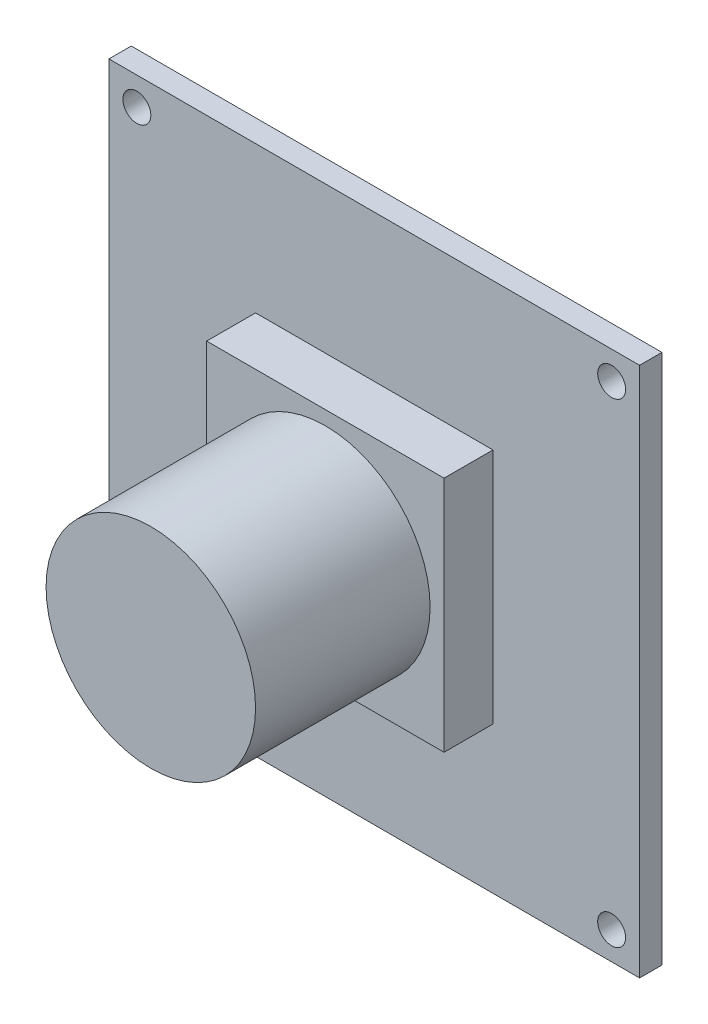
SolidWorks part; units mm, degrees
ref_plane "Front Plane" through (0, 0, 0) normal (0, 0, 1) x (1, 0, 0)
ref_plane "Top Plane" through (0, 0, 0) normal (0, 1, 0) x (1, 0, 0)
ref_plane "Right Plane" through (0, 0, 0) normal (1, 0, 0) x (0, 0, -1)
sketch "Sketch1" plane through (0, 0, 0) normal (0, 0, 1) x (1, 0, 0)
  line L1 (-19, -19) -> (19, -19)
  line L2 (-19, -19) -> (-19, 19)
  line L3 (-19, 19) -> (19, 19)
  line L4 (19, -19) -> (19, 19)
  line L5 (-19, -19) -> (19, 19) construction
  line L6 (-19, 19) -> (19, -19) construction
  point P0 (0, 0)
  dimension "D1" = 38
  dimension "D2" = 38
extrude "Boss-Extrude1" add sketch "Sketch1" against normal blind 1.6
sketch "Sketch2" plane through (0, 0, 0) normal (0, 0, 1) x (1, 0, 0)
  line L1 (-8.5, -8.5) -> (8.5, -8.5)
  line L2 (-8.5, -8.5) -> (-8.5, 8.5)
  line L3 (-8.5, 8.5) -> (8.5, 8.5)
  line L4 (8.5, -8.5) -> (8.5, 8.5)
  line L5 (-8.5, -8.5) -> (8.5, 8.5) construction
  line L6 (-8.5, 8.5) -> (8.5, -8.5) construction
  point P0 (0, 0)
  dimension "D1" = 17
  dimension "D2" = 17
extrude "Boss-Extrude2" add sketch "Sketch2" along normal blind 3.5
sketch "Sketch3" plane through (0, 0, 3.5) normal (0, 0, 1) x (1, 0, 0)
  circle A0 centre (0, 0) radius 7.5
  dimension "D1" = 15
extrude "Boss-Extrude3" add sketch "Sketch3" along normal blind 12.5
sketch "Sketch4" plane through (0, 0, 0) normal (0, 0, 1) x (1, 0, 0)
  line L0 (0, 0) -> (0, 19) construction
  line L1 (19, 19) -> (-19, 19) construction
  line L2 (0, 0) -> (19, 0) construction
  line L3 (19, -19) -> (19, 19) construction
  line L4 (-19, 19) -> (-19, -19) construction
  circle A0 centre (-17, 17) radius 1
  circle A1 centre (17, 17) radius 1
  circle A2 centre (-17, -17) radius 1
  circle A3 centre (17, -17) radius 1
  point P10 (0, 0)
  dimension "D1" = 2
  dimension "D2" = 2
  dimension "D3" = 2
extrude "Cut-Extrude1" cut sketch "Sketch4" against normal up to next
sketch "Sketch5" plane through (0, 0, -1.6) normal (0, 0, -1) x (-1, 0, 0)
  line L0 (-19, -19) -> (-19, 19) construction
  line L1 (-10, -16) -> (0, -16)
  line L2 (-10, -16) -> (-10, -11)
  line L3 (-10, -11) -> (0, -11)
  line L4 (0, -16) -> (0, -11)
  line L5 (-10, -16) -> (0, -11) construction
  line L6 (-10, -11) -> (0, -16) construction
  line L7 (19, -19) -> (-19, -19) construction
  point P0 (-5, -13.5)
  dimension "D1" = 9
  dimension "D2" = 3
  dimension "D3" = 5
  dimension "D4" = 10
extrude "Boss-Extrude4" add sketch "Sketch5" along normal blind 8
